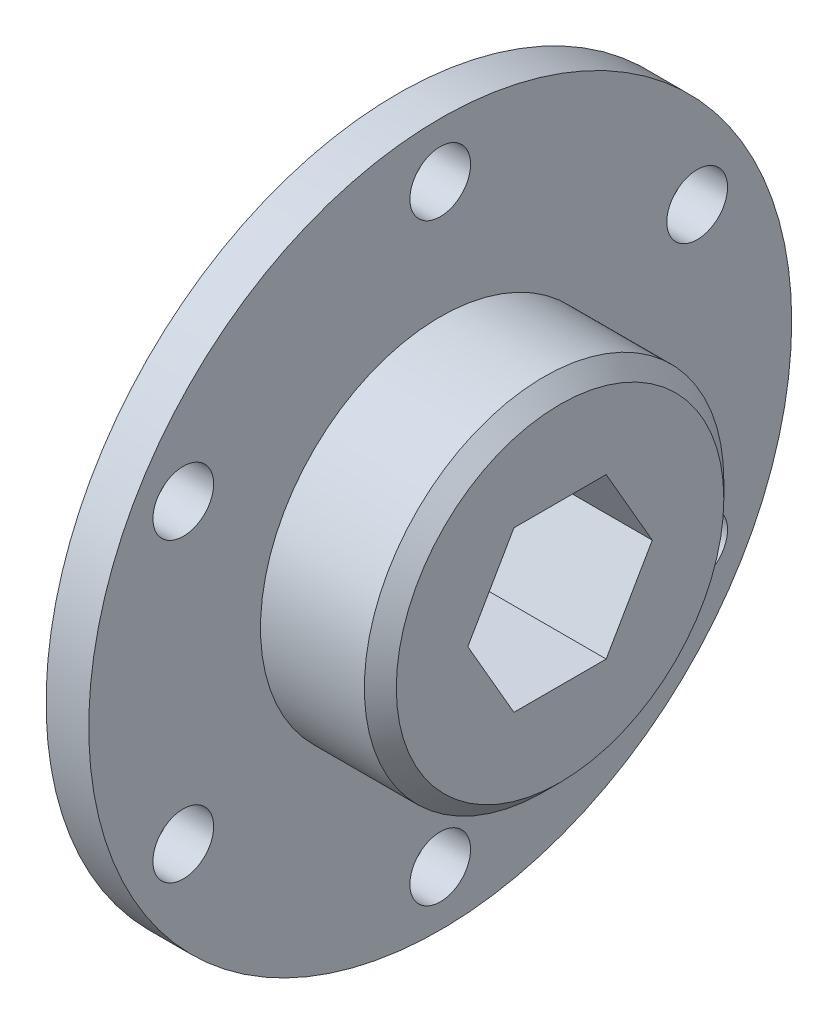
SolidWorks part; units mm, degrees
ref_plane "Front Plane" through (0, 0, 0) normal (0, 0, 1) x (1, 0, 0)
ref_plane "Top Plane" through (0, 0, 0) normal (0, 1, 0) x (1, 0, 0)
ref_plane "Right Plane" through (0, 0, 0) normal (1, 0, 0) x (0, 0, -1)
sketch "Sketch1" plane through (0, 0, 0) normal (1, 0, 0) x (0, 0, -1)
  line L0 (0, 27.94) -> (0, 25.9969) construction
  line L1 (7.3323, 0) -> (3.6662, 6.35)
  line L2 (3.6662, 6.35) -> (-3.6662, 6.35)
  line L3 (-3.6662, 6.35) -> (-7.3323, 0)
  line L4 (-7.3323, 0) -> (-3.6662, -6.35)
  line L5 (-3.6662, -6.35) -> (3.6662, -6.35)
  line L6 (3.6662, -6.35) -> (7.3323, 0)
  circle A0 centre (0, 0) radius 27.94
  circle A1 centre (0, 0) radius 6.35 construction
  circle A2 centre (0, 23.5839) radius 2.413
  circle A3 centre (20.4243, 11.792) radius 2.413
  circle A4 centre (20.4243, -11.7919) radius 2.413
  circle A5 centre (0, -23.5839) radius 2.413
  circle A6 centre (-20.4243, -11.792) radius 2.413
  circle A7 centre (-20.4243, 11.7919) radius 2.413
  point P27 (0, 0)
  dimension "D1" = 55.88
  dimension "D3" = 4.826
  dimension "D2" = 1.9431
  dimension "D4" = 6
extrude "Boss-Extrude1" add sketch "Sketch1" along normal blind 3.3909
sketch "Sketch2" plane through (3.3909, 0, 0) normal (1, 0, 0) x (0, 0, -1)
  line L0 (3.6662, -6.35) -> (7.3323, 0) construction
  line L1 (-3.6662, -6.35) -> (3.6662, -6.35) construction
  line L2 (-7.3323, 0) -> (-3.6662, -6.35) construction
  line L3 (-3.6662, 6.35) -> (-7.3323, 0) construction
  line L4 (3.6662, 6.35) -> (-3.6662, 6.35) construction
  line L5 (7.3323, 0) -> (3.6662, 6.35) construction
  line L6 (3.6662, -6.35) -> (7.3323, 0)
  line L7 (-3.6662, -6.35) -> (3.6662, -6.35)
  line L8 (-7.3323, 0) -> (-3.6662, -6.35)
  line L9 (-3.6662, 6.35) -> (-7.3323, 0)
  line L10 (3.6662, 6.35) -> (-3.6662, 6.35)
  line L11 (7.3323, 0) -> (3.6662, 6.35)
  circle A0 centre (0, 0) radius 14.2875
  dimension "D1" = 28.575
extrude "Boss-Extrude2" add sketch "Sketch2" along normal blind 9.525
chamfer "Chamfer1" distance 1.27 angle 45 1 edges at (12.9159, 0, -14.2875)
